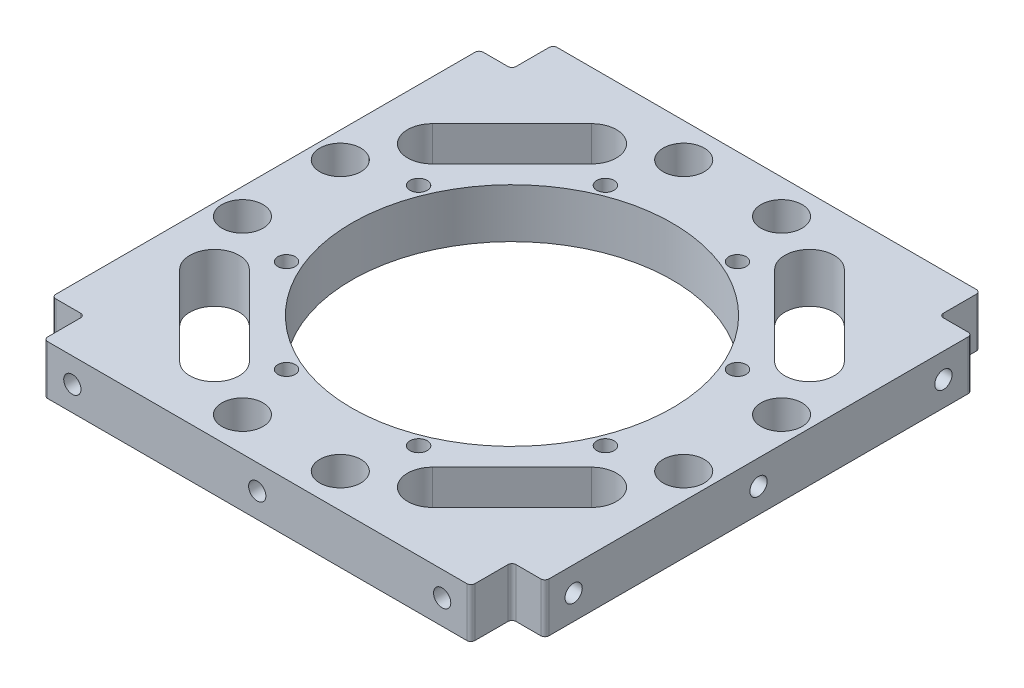
SolidWorks part; units mm, degrees
material "6063-O"
ref_plane "前视基准面" through (0, 0, 0) normal (0, 0, 1) x (1, 0, 0)
ref_plane "上视基准面" through (0, 0, 0) normal (0, 1, 0) x (1, 0, 0)
ref_plane "右视基准面" through (0, 0, 0) normal (1, 0, 0) x (0, 0, -1)
sketch "草图1" plane through (0, 0, 0) normal (0, 1, 0) x (1, 0, 0)
  line L1 (-60, 62) -> (60, 62)
  line L2 (-60, 62) -> (-60, -62)
  line L3 (-60, -62) -> (60, -62)
  line L4 (60, 62) -> (60, -62)
  line L5 (-60, 62) -> (60, -62) construction
  line L6 (-60, -62) -> (60, 62) construction
  circle A0 centre (0, 0) radius 39
  dimension "D1" = 78
  dimension "D2" = 120
  dimension "D3" = 124
extrude "凸台-拉伸1" add sketch "草图1" along normal mid plane 12
sketch "草图2" plane through (0, 6, 0) normal (0, 1, 0) x (1, 0, 0)
  line L0 (0, 0) -> (0, 42) construction
  line L1 (-16.0727, 38.8029) -> (0, 0) construction
  circle A0 centre (-16.0727, 38.8029) radius 2.1
  circle A1 centre (0, 0) radius 42 construction
  dimension "D1" = 84
  dimension "D2" = 4.2
  dimension "D3" = 22.5
extrude "切除-拉伸1" cut sketch "草图2" against normal through all
pattern_circular "阵列(圆周)1" count 8 over 360 about axis through (0, 0, 0) along (0, 1, 0) of "切除-拉伸1"
sketch "草图3" plane through (60, 0, 0) normal (1, 0, 0) x (0, 0, -1)
  line L0 (45, 0) -> (-45, 0) construction
  circle A0 centre (-45, 0) radius 1.5
  circle A1 centre (0, 0) radius 1.5
  circle A2 centre (45, 0) radius 1.5
  point P7 (0, 0)
  dimension "D3" = 3
  dimension "D1" = 90
extrude "切除-拉伸2" cut sketch "草图3" against normal blind 15
sketch "草图4" plane through (0, 0, -62) normal (0, 0, -1) x (-1, 0, 0)
  line L0 (-45, 0) -> (45, 0) construction
  circle A0 centre (-45, 0) radius 1.5
  circle A1 centre (0, 0) radius 1.5
  circle A2 centre (45, 0) radius 1.5
  point P3 (0, 0)
  dimension "D2" = 3
  dimension "D1" = 90
extrude "切除-拉伸5" cut sketch "草图4" against normal blind 10
hole_wizard "M5 螺纹孔1" positions "草图6" profile "草图7" tap size "M5" standard "ISO"
sketch "草图6" plane through (60, 0, 0) normal (1, 0, 0) x (0, 0, -1)
  point P0 (45, 0)
  point P3 (0, 0)
  point P6 (-45, 0)
sketch "草图7" plane through (60, 0, -45) normal (0, 1, 0) x (0, 0, -1)
  line L0 (0, 0) -> (0, 18.6618)
  line L1 (0, 18.6618) -> (2.1, 17.4)
  line L2 (2.1, 17.4) -> (2.1, 0)
  line L5 (2.1, 0) -> (0, 0)
  line L10 (0, 18.6618) -> (-2.1, 17.4) construction
  line L11 (0, -6.35) -> (0, 107.95) construction
  dimension "螺纹孔钻头直径" = 4.2
  dimension "螺纹孔钻头深度" = 17.4
  dimension "导头角度" = 118
cosmetic thread "孔螺蚊线1" parameters "D1"=15, "D2"=5
cosmetic thread "孔螺蚊线2" parameters "D1"=15, "D2"=5
cosmetic thread "孔螺蚊线3" parameters "D1"=15, "D2"=5
hole_wizard "M5 螺纹孔2" positions "草图8" profile "草图9" tap size "M5" standard "ISO"
sketch "草图8" plane through (0, 0, -62) normal (0, 0, -1) x (-1, 0, 0)
  point P0 (-45, 0)
  point P3 (0, 0)
  point P6 (45, 0)
sketch "草图9" plane through (45, 0, -62) normal (1, 0, 0) x (0, 1, 0)
  line L0 (0, 0) -> (0, 13.6618)
  line L1 (0, 13.6618) -> (2.1, 12.4)
  line L2 (2.1, 12.4) -> (2.1, 0)
  line L5 (2.1, 0) -> (0, 0)
  line L10 (0, 13.6618) -> (-2.1, 12.4) construction
  line L11 (0, -6.35) -> (0, 107.95) construction
  dimension "螺纹孔钻头直径" = 4.2
  dimension "螺纹孔钻头深度" = 12.4
  dimension "导头角度" = 118
cosmetic thread "孔螺蚊线7" parameters "D1"=10, "D2"=5
cosmetic thread "孔螺蚊线8" parameters "D1"=10, "D2"=5
cosmetic thread "孔螺蚊线9" parameters "D1"=10, "D2"=5
mirror "镜向1" about plane through (0, 0, 0) normal (1, 0, 0) of "M5 螺纹孔1", "切除-拉伸2"
cosmetic thread "孔螺蚊线4" parameters "D1"=15, "D2"=5
cosmetic thread "孔螺蚊线5" parameters "D1"=15, "D2"=5
cosmetic thread "孔螺蚊线6" parameters "D1"=15, "D2"=5
mirror "镜向2" about plane through (0, 0, 0) normal (0, 0, 1) of "M5 螺纹孔2", "切除-拉伸5"
cosmetic thread "孔螺蚊线10" parameters "D1"=10, "D2"=5
cosmetic thread "孔螺蚊线11" parameters "D1"=10, "D2"=5
cosmetic thread "孔螺蚊线12" parameters "D1"=10, "D2"=5
sketch "草图10" plane through (0, -6, 0) normal (0, -1, 0) x (1, 0, 0)
  line L1 (-60, 62) -> (-52, 62)
  line L2 (-60, 62) -> (-60, 52)
  line L3 (-60, 52) -> (-52, 52)
  line L4 (-52, 62) -> (-52, 52)
  line L5 (60, 62) -> (52, 62)
  line L6 (60, 62) -> (60, 52)
  line L7 (60, 52) -> (52, 52)
  line L8 (52, 62) -> (52, 52)
  line L9 (60, -62) -> (52, -62)
  line L10 (60, -62) -> (60, -52)
  line L11 (60, -52) -> (52, -52)
  line L12 (52, -62) -> (52, -52)
  line L13 (-60, -62) -> (-52, -62)
  line L14 (-60, -62) -> (-60, -52)
  line L15 (-60, -52) -> (-52, -52)
  line L16 (-52, -62) -> (-52, -52)
  dimension "D1" = 8
  dimension "D2" = 10
extrude "切除-拉伸6" cut sketch "草图10" against normal through all
hole_wizard "M5 螺纹孔3" positions "3D草图2" profile "草图11" tap size "M5" standard "ISO" end condition through all
sketch3d "3D草图2"
  line L0 (16.0727, -6, -38.8029) -> (16.0727, 6, -38.8029) construction
  line L1 (38.8029, -6, -16.0727) -> (38.8029, 6, -16.0727) construction
  line L2 (38.8029, -6, 16.0727) -> (38.8029, 6, 16.0727) construction
  line L3 (16.0727, -6, 38.8029) -> (16.0727, 6, 38.8029) construction
  line L4 (-16.0727, -6, 38.8029) -> (-16.0727, 6, 38.8029) construction
  line L5 (-38.8029, -6, 16.0727) -> (-38.8029, 6, 16.0727) construction
  line L6 (-38.8029, -6, -16.0727) -> (-38.8029, 6, -16.0727) construction
  line L7 (-16.0727, -6, -38.8029) -> (-16.0727, 6, -38.8029) construction
  point P0 (16.0727, 6, -38.8029)
  point P4 (38.8029, 6, -16.0727)
  point P8 (38.8029, 6, 16.0727)
  point P12 (16.0727, 6, 38.8029)
  point P16 (-16.0727, 6, 38.8029)
  point P20 (-38.8029, 6, 16.0727)
  point P24 (-38.8029, 6, -16.0727)
  point P28 (-16.0727, 6, -38.8029)
sketch "草图11" plane through (16.0727, 6, -38.8029) normal (1, 0, 0) x (0, 0, 1)
  line L0 (0, 0) -> (0, 12)
  line L1 (0, 12) -> (2.1, 12)
  line L2 (2.1, 12) -> (2.1, 0)
  line L5 (2.1, 0) -> (0, 0)
  line L11 (0, -6.35) -> (0, 107.95) construction
  dimension "通孔螺纹孔钻头直径" = 4.2
  dimension "通孔螺纹孔钻头深度" = 12
cosmetic thread "孔螺蚊线13" parameters "D2"=5
cosmetic thread "孔螺蚊线14" parameters "D2"=5
cosmetic thread "孔螺蚊线15" parameters "D2"=5
cosmetic thread "孔螺蚊线16" parameters "D2"=5
cosmetic thread "孔螺蚊线17" parameters "D2"=5
cosmetic thread "孔螺蚊线18" parameters "D2"=5
cosmetic thread "孔螺蚊线19" parameters "D2"=5
cosmetic thread "孔螺蚊线20" parameters "D2"=5
sketch "草图12" plane through (0, -6, 0) normal (0, -1, 0) x (1, 0, 0)
  line L0 (0, 0) -> (45.8993, -26.5) construction
  line L1 (0, 0) -> (53, 0) construction
  line L2 (0, 0) -> (26.5, -45.8993) construction
  line L3 (26.5, -45.8993) -> (45.8993, -26.5) construction
  line L4 (22.2574, -41.6567) -> (41.6567, -22.2574)
  line L5 (30.7426, -50.142) -> (50.142, -30.7426)
  circle A0 centre (0, 0) radius 53 construction
  arc A1 (22.2574, -41.6567) -> (30.7426, -50.142) centre (26.5, -45.8993) ccw
  arc A2 (50.142, -30.7426) -> (41.6567, -22.2574) centre (45.8993, -26.5) ccw
  point P6 (36.1997, -36.1997)
  dimension "D1" = 106
  dimension "D2" = 30
  dimension "D4" = 6
  dimension "D3" = 30
extrude "切除-拉伸7" cut sketch "草图12" against normal through all
pattern_circular "阵列(圆周)2" count 4 over 360 about axis through (0, 0, 0) along (0, 1, 0) of "切除-拉伸7"
sketch "草图13" plane through (0, -6, 0) normal (0, -1, 0) x (1, 0, 0)
  line L0 (0, 0) -> (-11.9042, 53.6963) construction
  line L1 (0, 0) -> (11.9042, 53.6963) construction
  line L2 (0, 0) -> (0, 39) construction
  circle A0 centre (0, 0) radius 55 construction
  circle A1 centre (0, 0) radius 39 construction
  circle A2 centre (11.9042, 53.6963) radius 5
  circle A3 centre (-11.9042, 53.6963) radius 5
  dimension "D1" = 110
  dimension "D4" = 10
  dimension "D2" = 25
  dimension "D3" = 12.5
extrude "切除-拉伸8" cut sketch "草图13" against normal through all
pattern_circular "阵列(圆周)3" count 4 over 360 about axis through (0, 0, 0) along (0, 1, 0) of "切除-拉伸8"
fillet "圆角1" radius 1 12 edges at (-52, 0, -52) (-52, 0, -62) (52, 0, -62) (52, 0, -52) (60, 0, -52) (52, 0, 62) (-52, 0, 62) (-52, 0, 52) (-60, 0, 52) (-60, 0, -52) (60, 0, 52) (52, 0, 52)
